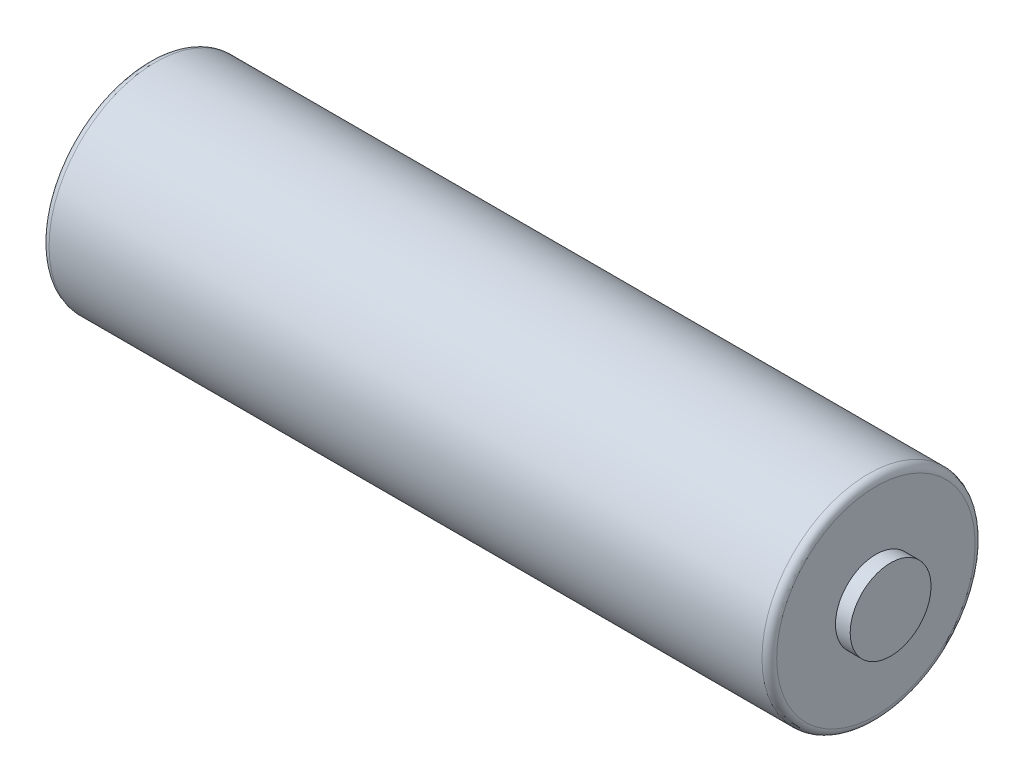
SolidWorks part; units mm, degrees
ref_plane "Front" through (0, 0, 0) normal (0, 0, 1) x (1, 0, 0)
ref_plane "Top" through (0, 0, 0) normal (0, 1, 0) x (1, 0, 0)
ref_plane "Right" through (0, 0, 0) normal (1, 0, 0) x (0, 0, -1)
sketch "Sketch2" plane through (0, 0, 0) normal (0, 0, 1) x (1, 0, 0)
  line L0 (0, 0) -> (76.4598, 0) construction
  line L1 (0, 0) -> (0, 7.25)
  line L2 (0, 7.25) -> (49.5, 7.25)
  line L3 (49.5, 7.25) -> (49.5, 2.75)
  line L4 (49.5, 2.75) -> (50.5, 2.75)
  line L5 (50.5, 2.75) -> (50.5, 0)
  line L6 (50.5, 0) -> (0, 0)
  dimension "D1" = 14.5
  dimension "D2" = 5.5
  dimension "D3" = 1
  dimension "D4" = 50.5
revolve "Revolve1" add sketch "Sketch2" angle 360 about L0
fillet "Fillet1" radius 0.5 2 edges at (49.5, 0, 7.25) (0, 0, 7.25)
